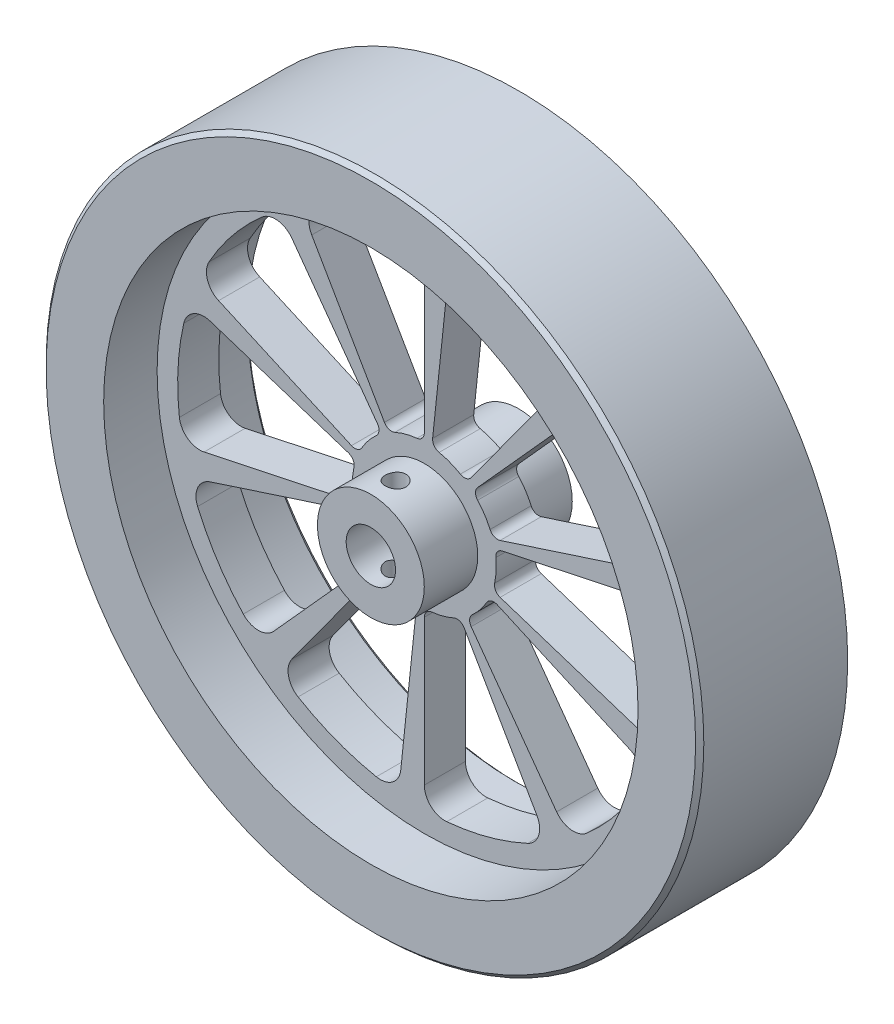
SolidWorks part; units mm, degrees
ref_plane "Front Plane" through (0, 0, 0) normal (0, 0, 1) x (1, 0, 0)
ref_plane "Top Plane" through (0, 0, 0) normal (0, 1, 0) x (1, 0, 0)
ref_plane "Right Plane" through (0, 0, 0) normal (1, 0, 0) x (0, 0, -1)
sketch "Sketch1" plane through (0, 0, 0) normal (0, 0, 1) x (1, 0, 0)
  circle A0 centre (0, 0) radius 80
  circle A1 centre (0, 0) radius 6
  dimension "D1" = 160
  dimension "D2" = 12
extrude "Boss-Extrude1" add sketch "Sketch1" along normal mid plane 36
sketch "Sketch2" plane through (0, 0, 18) normal (0, 0, 1) x (1, 0, 0)
  circle A0 centre (0, 0) radius 65
  circle A1 centre (0, 0) radius 13
  dimension "D1" = 130
  dimension "D2" = 26
extrude "Cut-Extrude1" cut sketch "Sketch2" against normal blind 13
mirror "Mirror1" about plane through (0, 0, 0) normal (0, 0, 1) of "Cut-Extrude1"
sketch "Sketch3" plane through (0, 0, 5) normal (0, 0, 1) x (1, 0, 0)
  line L0 (0, 19.3972) -> (0, 54.7723)
  line L1 (-9.6986, 16.7984) -> (-27.3861, 47.4342)
  line L2 (2.0276, 19.2909) -> (5.7253, 54.4722)
  line L3 (11.4014, 15.6926) -> (32.1943, 44.3117)
  line L4 (12.9792, 14.4149) -> (36.6498, 40.7037)
  line L5 (18.4478, 5.9941) -> (52.0915, 16.9256)
  line L6 (18.9733, 4.0329) -> (53.5754, 11.3878)
  line L7 (18.4478, -5.9941) -> (52.0915, -16.9256)
  line L8 (17.7202, -7.8895) -> (50.0369, -22.2779)
  line L9 (11.4014, -15.6926) -> (32.1943, -44.3117)
  line L10 (9.6986, -16.7984) -> (27.3861, -47.4342)
  line L11 (0, -19.3972) -> (0, -54.7723)
  line L12 (-2.0276, -19.2909) -> (-5.7253, -54.4722)
  line L13 (-11.4014, -15.6926) -> (-32.1943, -44.3117)
  line L14 (-12.9792, -14.4149) -> (-36.6498, -40.7037)
  line L15 (-18.4478, -5.9941) -> (-52.0915, -16.9256)
  line L16 (-18.9733, -4.0329) -> (-53.5754, -11.3878)
  line L17 (-18.4478, 5.9941) -> (-52.0915, 16.9256)
  line L18 (-17.7202, 7.8895) -> (-50.0369, 22.2779)
  line L19 (-11.4014, 15.6926) -> (-32.1943, 44.3117)
  arc A0 (-5.4545, 59.7516) -> (-25.152, 54.4736) centre (0, 0) ccw
  arc A1 (-1.7949, 17.4077) -> (-7.1495, 15.973) centre (0, 0) ccw
  arc A2 (0, 54.7723) -> (-5.4545, 59.7516) centre (-5, 54.7723) ccw
  arc A3 (-27.3861, 47.4342) -> (-25.152, 54.4736) centre (-23.056, 49.9342) cw
  arc A4 (-9.6986, 16.7984) -> (-7.1495, 15.973) centre (-7.9665, 17.7984) ccw
  arc A5 (0, 19.3972) -> (-1.7949, 17.4077) centre (-2, 19.3972) cw
  arc A6 (8.7799, 15.1381) -> (3.6046, 17.1247) centre (0, 0) ccw
  arc A7 (11.4014, 15.6926) -> (8.7799, 15.1381) centre (9.7833, 16.8682) cw
  arc A8 (2.0276, 19.2909) -> (3.6046, 17.1247) centre (4.0166, 19.0818) ccw
  arc A9 (5.7253, 54.4722) -> (11.6704, 58.8541) centre (10.6979, 53.9496) cw
  arc A10 (30.7083, 51.5461) -> (11.6704, 58.8541) centre (0, 0) ccw
  arc A11 (32.1943, 44.3117) -> (30.7083, 51.5461) centre (28.1492, 47.2506) ccw
  arc A12 (16.0011, 7.0863) -> (12.9819, 11.7354) centre (0, 0) ccw
  arc A13 (18.4478, 5.9941) -> (16.0011, 7.0863) centre (17.8298, 7.8962) cw
  arc A14 (12.9792, 14.4149) -> (12.9819, 11.7354) centre (14.4655, 13.0766) ccw
  arc A15 (36.6498, 40.7037) -> (44.0351, 40.7543) centre (40.3655, 37.3581) cw
  arc A16 (55.1416, 23.6518) -> (44.0351, 40.7543) centre (0, 0) ccw
  arc A17 (52.0915, 16.9256) -> (55.1416, 23.6518) centre (50.5464, 21.6808) ccw
  arc A18 (17.1104, -3.6723) -> (17.4005, 1.8636) centre (0, 0) ccw
  arc A19 (18.4478, -5.9941) -> (17.1104, -3.6723) centre (19.0658, -4.0919) cw
  arc A20 (18.9733, 4.0329) -> (17.4005, 1.8636) centre (19.3891, 2.0766) ccw
  arc A21 (53.5754, 11.3878) -> (59.5799, 7.0877) centre (54.6149, 6.4971) cw
  arc A22 (58.5126, -13.2767) -> (59.5799, 7.0877) centre (0, 0) ccw
  arc A23 (52.0915, -16.9256) -> (58.5126, -13.2767) centre (53.6366, -12.1703) ccw
  arc A24 (11.6841, -13.0281) -> (15.1727, -8.7201) centre (0, 0) ccw
  arc A25 (11.4014, -15.6926) -> (11.6841, -13.0281) centre (13.0194, -14.5171) cw
  arc A26 (17.7202, -7.8895) -> (15.1727, -8.7201) centre (16.9067, -9.7166) ccw
  arc A27 (50.0369, -22.2779) -> (52.3672, -29.2861) centre (48.0033, -26.8456) cw
  arc A28 (39.5339, -45.1339) -> (52.3672, -29.2861) centre (0, 0) ccw
  arc A29 (32.1943, -44.3117) -> (39.5339, -45.1339) centre (36.2394, -41.3728) ccw
  arc A30 (1.7949, -17.4077) -> (7.1495, -15.973) centre (0, 0) ccw
  arc A31 (0, -19.3972) -> (1.7949, -17.4077) centre (2, -19.3972) cw
  arc A32 (9.6986, -16.7984) -> (7.1495, -15.973) centre (7.9665, -17.7984) ccw
  arc A33 (27.3861, -47.4342) -> (25.152, -54.4736) centre (23.056, -49.9342) cw
  arc A34 (5.4545, -59.7516) -> (25.152, -54.4736) centre (0, 0) ccw
  arc A35 (0, -54.7723) -> (5.4545, -59.7516) centre (5, -54.7723) ccw
  arc A36 (-8.7799, -15.1381) -> (-3.6046, -17.1247) centre (0, 0) ccw
  arc A37 (-11.4014, -15.6926) -> (-8.7799, -15.1381) centre (-9.7833, -16.8682) cw
  arc A38 (-2.0276, -19.2909) -> (-3.6046, -17.1247) centre (-4.0166, -19.0818) ccw
  arc A39 (-5.7253, -54.4722) -> (-11.6704, -58.8541) centre (-10.6979, -53.9496) cw
  arc A40 (-30.7083, -51.5461) -> (-11.6704, -58.8541) centre (0, 0) ccw
  arc A41 (-32.1943, -44.3117) -> (-30.7083, -51.5461) centre (-28.1492, -47.2506) ccw
  arc A42 (-16.0011, -7.0863) -> (-12.9819, -11.7354) centre (0, 0) ccw
  arc A43 (-18.4478, -5.9941) -> (-16.0011, -7.0863) centre (-17.8298, -7.8962) cw
  arc A44 (-12.9792, -14.4149) -> (-12.9819, -11.7354) centre (-14.4655, -13.0766) ccw
  arc A45 (-36.6498, -40.7037) -> (-44.0351, -40.7543) centre (-40.3655, -37.3581) cw
  arc A46 (-55.1416, -23.6518) -> (-44.0351, -40.7543) centre (0, 0) ccw
  arc A47 (-52.0915, -16.9256) -> (-55.1416, -23.6518) centre (-50.5464, -21.6808) ccw
  arc A48 (-17.1104, 3.6723) -> (-17.4005, -1.8636) centre (0, 0) ccw
  arc A49 (-18.4478, 5.9941) -> (-17.1104, 3.6723) centre (-19.0658, 4.0919) cw
  arc A50 (-18.9733, -4.0329) -> (-17.4005, -1.8636) centre (-19.3891, -2.0766) ccw
  arc A51 (-53.5754, -11.3878) -> (-59.5799, -7.0877) centre (-54.6149, -6.4971) cw
  arc A52 (-58.5126, 13.2767) -> (-59.5799, -7.0877) centre (0, 0) ccw
  arc A53 (-52.0915, 16.9256) -> (-58.5126, 13.2767) centre (-53.6366, 12.1703) ccw
  arc A54 (-11.6841, 13.0281) -> (-15.1727, 8.7201) centre (0, 0) ccw
  arc A55 (-11.4014, 15.6926) -> (-11.6841, 13.0281) centre (-13.0194, 14.5171) cw
  arc A56 (-17.7202, 7.8895) -> (-15.1727, 8.7201) centre (-16.9067, 9.7166) ccw
  arc A57 (-50.0369, 22.2779) -> (-52.3672, 29.2861) centre (-48.0033, 26.8456) cw
  arc A58 (-39.5339, 45.1339) -> (-52.3672, 29.2861) centre (0, 0) ccw
  arc A59 (-32.1943, 44.3117) -> (-39.5339, 45.1339) centre (-36.2394, 41.3728) ccw
  point P11 (0, 60)
  point P126 (0, 0)
  dimension "D1" = 120
  dimension "D2" = 35
  dimension "D4" = 5
  dimension "D5" = 2
  dimension "D3" = 30
  dimension "D6" = 10
extrude "Cut-Extrude3" cut sketch "Sketch3" against normal through all
chamfer "Chamfer1" distance 1 angle 45 2 edges at (65, 0, -18) (80, 0, 18)
sketch "Sketch4" plane through (0, 0, 0) normal (0, 1, 0) x (1, 0, 0)
  line L0 (-79, -18) -> (79, -18) construction
  circle A0 centre (0, -12) radius 2.5
  dimension "D2" = 5
  dimension "D1" = 6
extrude "Cut-Extrude4" cut sketch "Sketch4" against normal mid plane 26
